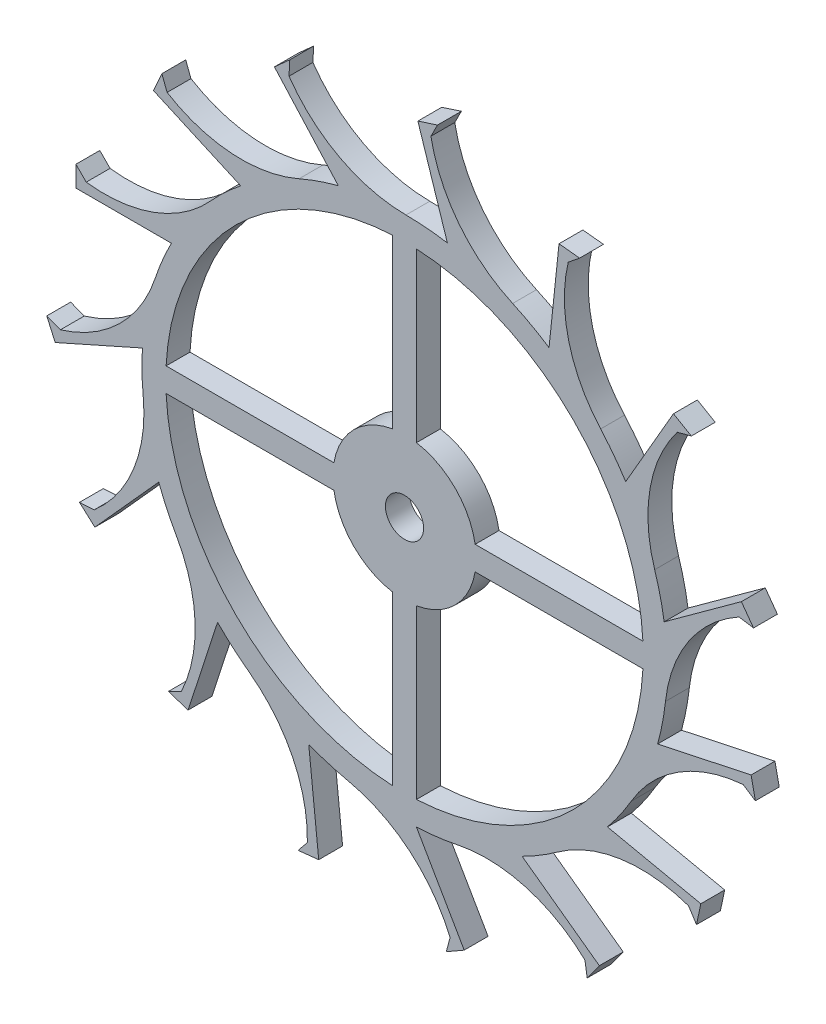
SolidWorks part; units mm, degrees
ref_plane "Alzado" through (0, 0, 0) normal (0, 0, 1) x (1, 0, 0)
ref_plane "Planta" through (0, 0, 0) normal (0, 1, 0) x (1, 0, 0)
ref_plane "Vista lateral" through (0, 0, 0) normal (1, 0, 0) x (0, 0, -1)
sketch "Croquis1" plane through (0, 0, 0) normal (0, 0, 1) x (1, 0, 0)
  line L0 (-2.75, 0) -> (2.75, 0) construction
  line L1 (0, -2.75) -> (0, 2.75) construction
  line L2 (0.125, -2.75) -> (0.125, -2.7472)
  line L3 (-2.75, -0.125) -> (-2.7472, -0.125)
  line L4 (-0.125, -2.75) -> (-0.125, -2.7472)
  line L5 (-2.75, 0.125) -> (-2.7472, 0.125)
  line L6 (0.125, 2.7472) -> (0.125, 2.75)
  line L7 (-0.125, 2.7472) -> (-0.125, 2.75)
  line L8 (0.125, -2.75) -> (0.125, 2.75) construction
  line L9 (2.7472, 0.125) -> (2.75, 0.125)
  line L10 (-0.125, -2.75) -> (-0.125, 2.75) construction
  line L11 (2.7472, -0.125) -> (2.75, -0.125)
  line L12 (-2.75, 0.125) -> (2.75, 0.125) construction
  line L13 (-0.125, -2.4969) -> (-0.125, -0.7395)
  line L14 (-2.75, -0.125) -> (2.75, -0.125) construction
  line L15 (0.125, -2.4969) -> (0.125, -0.7395)
  line L16 (-2.4969, 0.125) -> (-0.7395, 0.125)
  line L17 (-2.4969, -0.125) -> (-0.7395, -0.125)
  line L18 (0.125, 0.7395) -> (0.125, 2.4969)
  line L19 (-0.125, 0.7395) -> (-0.125, 2.4969)
  line L24 (0.7395, -0.125) -> (2.4969, -0.125)
  line L25 (0.7395, 0.125) -> (2.4969, 0.125)
  arc A0 (-0.125, 0.7395) -> (-0.7395, 0.125) centre (0, 0) ccw
  circle A1 centre (0, 0) radius 0.2
  arc A2 (-0.125, 2.4969) -> (-2.4969, 0.125) centre (0, 0) ccw
  circle A3 centre (0, 0) radius 2.75
  arc A4 (2.4969, 0.125) -> (0.125, 2.4969) centre (0, 0) ccw
  arc A5 (0.125, -2.4969) -> (2.4969, -0.125) centre (0, 0) ccw
  arc A6 (-2.4969, -0.125) -> (-0.125, -2.4969) centre (0, 0) ccw
  arc A7 (0.7395, 0.125) -> (0.125, 0.7395) centre (0, 0) ccw
  arc A8 (0.125, -0.7395) -> (0.7395, -0.125) centre (0, 0) ccw
  arc A9 (-0.7395, -0.125) -> (-0.125, -0.7395) centre (0, 0) ccw
  dimension "D1" = 5.5
  dimension "D2" = 5
  dimension "D3" = 0.4
  dimension "D4" = 1.5
  dimension "D5" = 0.125
  dimension "D6" = 0.125
extrude "Saliente-Extruir1" add sketch "Croquis1" along normal blind 0.25 contours A3 L15 A8 L24 A5 A2 L19 A0 L16 A1 L25 A7 L18 A4 L17 A9 L13 A6
sketch "Croquis2" plane through (0, 0, 0) normal (0, 0, -1) x (-1, 0, 0)
  line L0 (0, 0) -> (0, -3.991) construction
  line L1 (-0.125, -2.4969) -> (-0.125, -0.7395) construction
  line L2 (-0.625, -3.6132) -> (-0.4375, -3.7214)
  line L3 (-0.125, -2.7472) -> (-0.625, -3.6132)
  line L4 (0.125, -2.7472) -> (-0.4375, -3.7214) construction
  line L5 (0.125, -2.4969) -> (0.125, -0.7395) construction
  line L6 (-0.4375, -3.7214) -> (-0.4771, -3.5736)
  line L7 (-0.5313, -3.6673) -> (0.3135, -2.2041) construction
  line L8 (0, 0) -> (1.4554, -3.7148) construction
  line L9 (0, 0) -> (-0.125, -2.7472) construction
  circle A0 centre (0, 0) radius 2.75 construction
  arc A1 (-0.125, -2.7472) -> (0.5868, -2.6867) centre (0, 0) ccw
  arc A2 (0.5868, -2.6867) -> (-0.4771, -3.5736) centre (0.9068, -4.1521) ccw
  point P10 (1.0032, -2.5605)
  dimension "D2" = 1
  dimension "D1" = 30
  dimension "D5" = 1.5
  dimension "D3" = 45
  dimension "D4" = 24
extrude "Saliente-Extruir2" add sketch "Croquis2" against normal up to surface (0.25 mm away) up to face at (1.0103, -1.0103, 0.25)
pattern_circular "MatrizC1" count 15 over 360 about axis through (0, 0, 0) along (0, 0, 1) of "Saliente-Extruir2"
